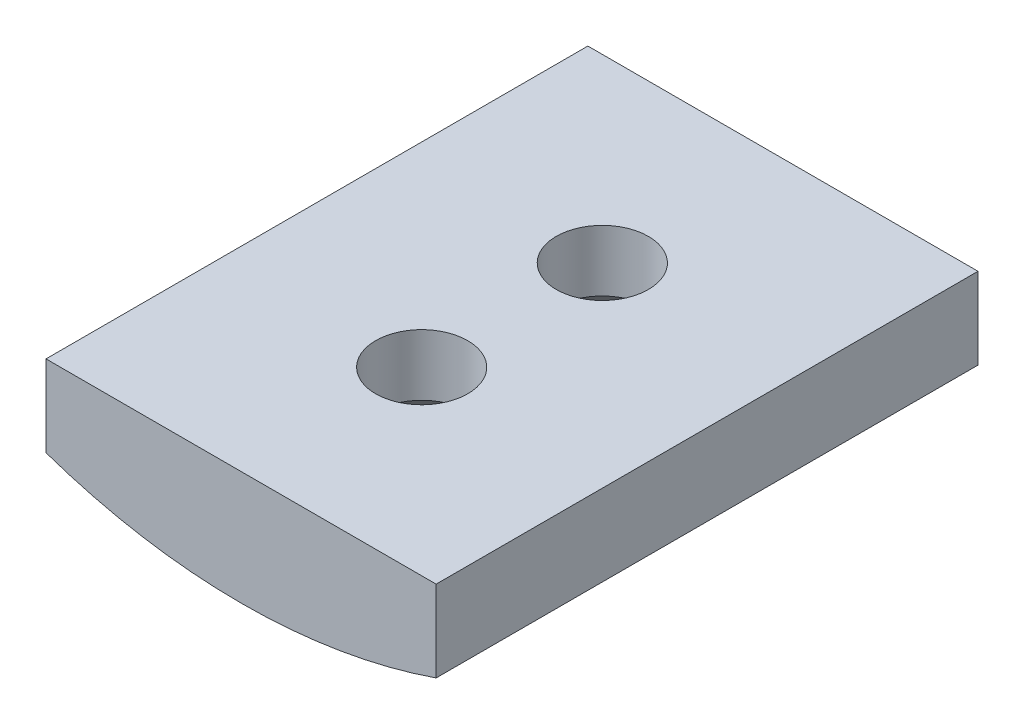
SolidWorks part; units mm, degrees
material "Gomma"
ref_plane "Piano frontale" through (0, 0, 0) normal (0, 0, 1) x (1, 0, 0)
ref_plane "Piano superiore" through (0, 0, 0) normal (0, 1, 0) x (1, 0, 0)
ref_plane "Piano destro" through (0, 0, 0) normal (1, 0, 0) x (0, 0, -1)
sketch "Schizzo1" plane through (0, 0, 0) normal (0, 0, 1) x (1, 0, 0)
  line L0 (0.5, -0.866) -> (-14.2224, -9.366) construction
  line L1 (-0.5, -0.866) -> (14.2224, -9.366) construction
  line L2 (-7.2, -15.4) -> (7.2, -15.4) construction
  line L3 (7.2, -15.4) -> (-7.2, -15.4) construction
  line L4 (7.2, -15.4) -> (7.2, -4.1569) construction
  line L5 (7.2, -4.1569) -> (-7.2, -4.1569) construction
  line L6 (-7.2, -15.4) -> (-7.2, -4.1569) construction
  line L7 (-9.3227, -14.2158) -> (-7.2, -15.4) construction
  line L8 (0, 0) -> (-14.7224, -8.5) construction
  line L9 (0, 0) -> (14.7224, -8.5) construction
  line L10 (0, 17) -> (0, 0) construction
  line L11 (7.2, -12.4) -> (-7.2, -12.4) construction
  line L12 (0.5, -0.866) -> (-14.2224, -9.366)
  line L13 (-0.5, -0.866) -> (14.2224, -9.366)
  line L14 (-7.2, -15.4) -> (7.2, -15.4)
  line L15 (7.2, -15.4) -> (-7.2, -15.4)
  line L16 (7.2, -15.4) -> (7.2, -4.1569)
  line L17 (7.2, -4.1569) -> (-7.2, -4.1569)
  line L18 (-7.2, -15.4) -> (-7.2, -4.1569)
  line L19 (-9.3227, -14.2158) -> (-7.2, -15.4)
  line L20 (0, 0) -> (-14.7224, -8.5)
  line L21 (0, 0) -> (14.7224, -8.5)
  line L22 (0, 17) -> (0, 0)
  line L23 (7.2, -12.4) -> (-7.2, -12.4)
  circle A0 centre (0, 5.4546) radius 22.0625
  circle A1 centre (0, 0) radius 17
  circle A2 centre (0, 0) radius 17
  dimension "D2" = 44.125
  dimension "D1" = 0
extrude "Estrusione-Estrusione1" add sketch "Schizzo1" against normal up to vertex (20 mm away) contours L16 L23 L18 L14 | L14 A0 | A2
ref_plane "Piano4" through (0, -16.6079, 0) normal (0, -1, 0) x (-1, 0, 0)
sketch "Schizzo2" plane through (0, -16.6079, 0) normal (0, -1, 0) x (-1, 0, 0)
  circle A0 centre (0, 13.3333) radius 3.15 construction
  circle A1 centre (0, 6.6667) radius 3.15 construction
  circle A2 centre (0, 13.3333) radius 3.15
  circle A3 centre (0, 6.6667) radius 3.15
extrude "Taglio-Estrusione1" cut sketch "Schizzo2" against normal blind 0.5
sketch "Schizzo3" plane through (0, -16.1079, 0) normal (0, -1, 0) x (1, 0, 0)
  point P0 (0, -6.6667)
  point P1 (0, -13.3333)
hole_wizard "Foro svasato per Vite M3-1" positions "Schizzo3D1" profile "Schizzo5" countersink size "M3" standard "ISO" end condition through all
sketch3d "Schizzo3D1"
  point P0 (0, -16.1079, -6.6667)
  point P3 (0, -16.1079, -13.3333)
sketch "Schizzo5" plane through (0, -16.1079, -6.6667) normal (1, 0, 0) x (0, 0, -1)
  line L0 (0, 0) -> (0, 3.7079)
  line L1 (0, 3.7079) -> (1.7, 3.7079)
  line L2 (1.7, 3.7079) -> (1.7, 1.45)
  line L3 (1.7, 1.45) -> (3.15, 0)
  line L5 (3.15, 0) -> (0, 0)
  line L6 (-1.7, 1.45) -> (-3.15, 0) construction
  line L11 (0, -6.35) -> (0, 107.95) construction
  dimension "Thru Hole Dia." = 3.4
  dimension "Thru Hole Depth" = 3.7079
  dimension "Near C'Sink Dia." = 6.3
  dimension "Near C'Sink Angle" = 90
